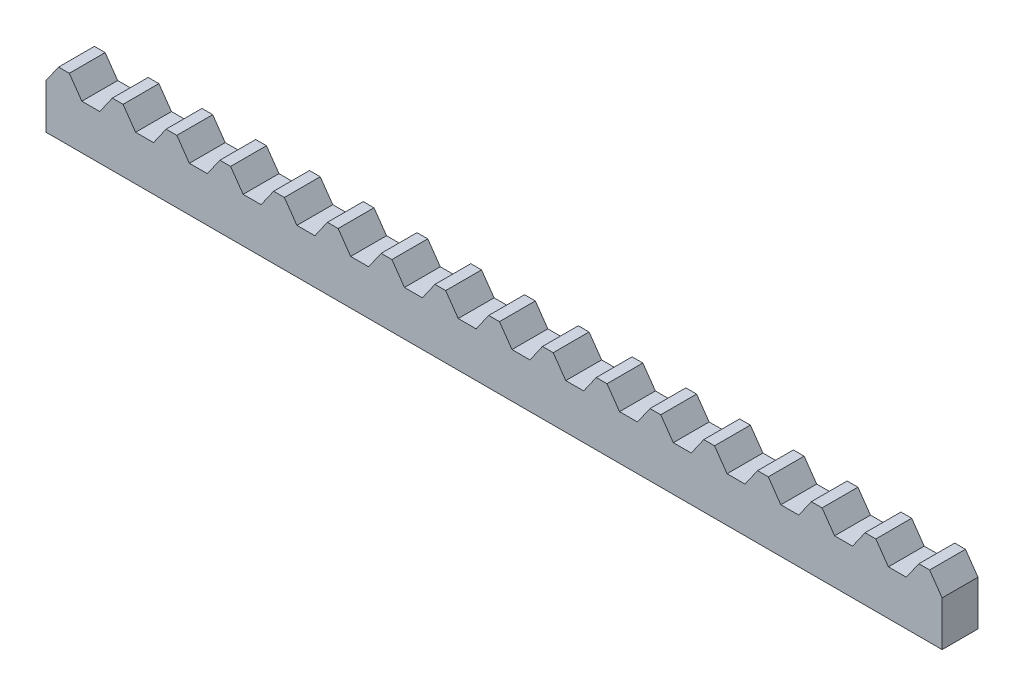
SolidWorks part; units mm, degrees
ref_plane "Front Plane" through (0, 0, 0) normal (0, 0, 1) x (1, 0, 0)
ref_plane "Top Plane" through (0, 0, 0) normal (0, 1, 0) x (1, 0, 0)
ref_plane "Right Plane" through (0, 0, 0) normal (1, 0, 0) x (0, 0, -1)
sketch "Sketch2" plane through (0, 0, 0) normal (0, 1, 0) x (1, 0, 0)
  line L1 (-50, -2) -> (50, -2)
  line L2 (-50, -2) -> (-50, 2)
  line L3 (-50, 2) -> (50, 2)
  line L4 (50, -2) -> (50, 2)
  line L5 (-50, -2) -> (50, 2) construction
  line L6 (-50, 2) -> (50, -2) construction
  point P0 (0, 0)
  dimension "D1" = 100
  dimension "D2" = 4
extrude "Boss-Extrude1" add sketch "Sketch2" along normal blind 5
sketch "Sketch3" plane through (0, 0, 2) normal (0, 0, 1) x (1, 0, 0)
  line L0 (-50, 5) -> (-46, 5)
  line L1 (-50, 5) -> (50, 5) construction
  line L2 (-46, 5) -> (-47.4, 7)
  line L3 (-47.4, 7) -> (-48.6, 7)
  line L4 (-48.6, 7) -> (-50, 5)
  line L5 (-42.6, 7) -> (-44, 5)
  line L6 (-44, 5) -> (-40, 5)
  line L7 (-40, 5) -> (-41.4, 7)
  line L8 (-41.4, 7) -> (-42.6, 7)
  line L9 (-36.6, 7) -> (-38, 5)
  line L10 (-38, 5) -> (-34, 5)
  line L11 (-34, 5) -> (-35.4, 7)
  line L12 (-35.4, 7) -> (-36.6, 7)
  line L13 (-30.6, 7) -> (-32, 5)
  line L14 (-32, 5) -> (-28, 5)
  line L15 (-28, 5) -> (-29.4, 7)
  line L16 (-29.4, 7) -> (-30.6, 7)
  line L17 (-24.6, 7) -> (-26, 5)
  line L18 (-26, 5) -> (-22, 5)
  line L19 (-22, 5) -> (-23.4, 7)
  line L20 (-23.4, 7) -> (-24.6, 7)
  line L21 (-18.6, 7) -> (-20, 5)
  line L22 (-20, 5) -> (-16, 5)
  line L23 (-16, 5) -> (-17.4, 7)
  line L24 (-17.4, 7) -> (-18.6, 7)
  line L25 (-12.6, 7) -> (-14, 5)
  line L26 (-14, 5) -> (-10, 5)
  line L27 (-10, 5) -> (-11.4, 7)
  line L28 (-11.4, 7) -> (-12.6, 7)
  line L29 (-6.6, 7) -> (-8, 5)
  line L30 (-8, 5) -> (-4, 5)
  line L31 (-4, 5) -> (-5.4, 7)
  line L32 (-5.4, 7) -> (-6.6, 7)
  line L33 (-0.6, 7) -> (-2, 5)
  line L34 (-2, 5) -> (2, 5)
  line L35 (2, 5) -> (0.6, 7)
  line L36 (0.6, 7) -> (-0.6, 7)
  line L37 (5.4, 7) -> (4, 5)
  line L38 (4, 5) -> (8, 5)
  line L39 (8, 5) -> (6.6, 7)
  line L40 (6.6, 7) -> (5.4, 7)
  line L41 (11.4, 7) -> (10, 5)
  line L42 (10, 5) -> (14, 5)
  line L43 (14, 5) -> (12.6, 7)
  line L44 (12.6, 7) -> (11.4, 7)
  line L45 (17.4, 7) -> (16, 5)
  line L46 (16, 5) -> (20, 5)
  line L47 (20, 5) -> (18.6, 7)
  line L48 (18.6, 7) -> (17.4, 7)
  line L49 (23.4, 7) -> (22, 5)
  line L50 (22, 5) -> (26, 5)
  line L51 (26, 5) -> (24.6, 7)
  line L52 (24.6, 7) -> (23.4, 7)
  line L53 (29.4, 7) -> (28, 5)
  line L54 (28, 5) -> (32, 5)
  line L55 (32, 5) -> (30.6, 7)
  line L56 (30.6, 7) -> (29.4, 7)
  line L57 (35.4, 7) -> (34, 5)
  line L58 (34, 5) -> (38, 5)
  line L59 (38, 5) -> (36.6, 7)
  line L60 (36.6, 7) -> (35.4, 7)
  line L61 (41.4, 7) -> (40, 5)
  line L62 (40, 5) -> (44, 5)
  line L63 (44, 5) -> (42.6, 7)
  line L64 (42.6, 7) -> (41.4, 7)
  line L65 (47.4, 7) -> (46, 5)
  line L66 (46, 5) -> (50, 5)
  line L67 (50, 5) -> (48.6, 7)
  line L68 (48.6, 7) -> (47.4, 7)
  point P6 (-48, 7)
  point P8 (-48, 5)
  dimension "D1" = 1.2
  dimension "D2" = 4
  dimension "D3" = 2
  dimension "D5" = 2
  dimension "D7" = 2
  dimension "D9" = 2
  dimension "D4" = 8
  dimension "D6" = 9
  dimension "D8" = 2
extrude "Boss-Extrude2" add sketch "Sketch3" against normal blind 4
